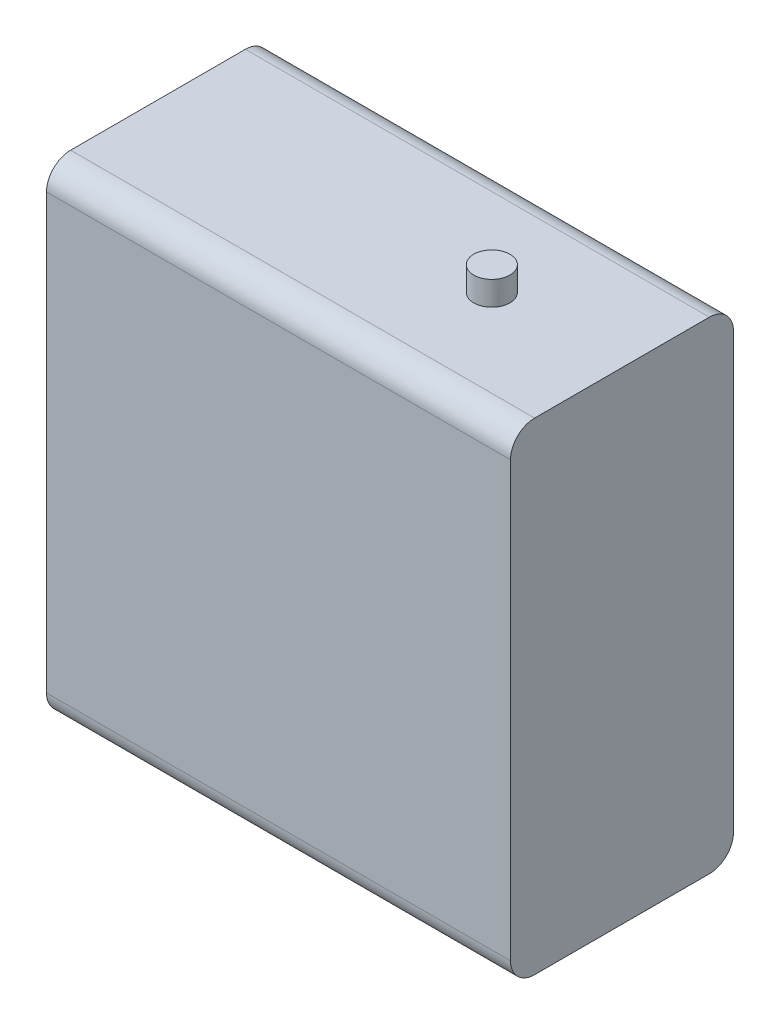
SolidWorks part; units mm, degrees
material "Nickel silver 65-12, UNS C75700"
ref_plane "前视基准面" through (0, 0, 0) normal (0, 0, 1) x (1, 0, 0)
ref_plane "上视基准面" through (0, 0, 0) normal (0, 1, 0) x (1, 0, 0)
ref_plane "右视基准面" through (0, 0, 0) normal (1, 0, 0) x (0, 0, -1)
other "Configuration Table"
sketch "Sketch2" plane through (0, 0, 0) normal (0, 0, 1) x (1, 0, 0)
  line L1 (0, 0) -> (38.5, 0)
  line L2 (0, 0) -> (0, 40)
  line L3 (0, 40) -> (38.5, 40)
  line L4 (38.5, 0) -> (38.5, 40)
  dimension "D1" = 38.5
  dimension "D2" = 40
extrude "Boss-Extrude1" add sketch "Sketch2" along normal blind 18.5
fillet "Fillet1" radius 2 4 edges at (19.25, 0, 0) (19.25, 0, 18.5) (19.25, 40, 18.5) (19.25, 40, 0)
sketch "Sketch3" plane through (0, 40, 0) normal (0, 1, 0) x (1, 0, 0)
  line L1 (38.5, -16.5) -> (38.5, -2) construction
  circle A0 centre (27.7, -9.25) radius 1.5
  point P6 (38.5, -9.25)
  dimension "D2" = 3
  dimension "D1" = 10.8
extrude "Boss-Extrude2" add sketch "Sketch3" along normal blind 2
sketch "Sketch4" plane through (0, 42, 0) normal (0, 1, 0) x (1, 0, 0)
  circle A0 centre (27.7, -9.25) radius 11
  dimension "D1" = 22
